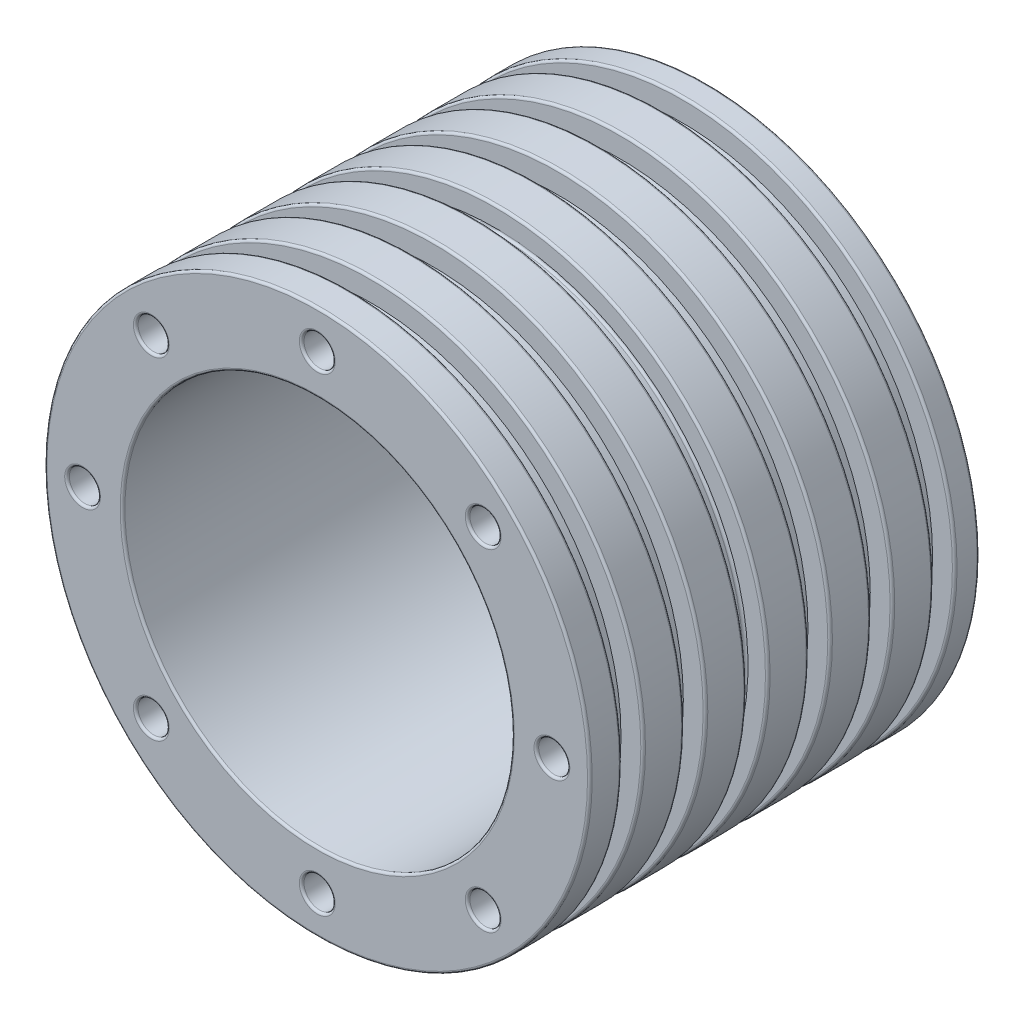
SolidWorks part; units mm, degrees
ref_plane "Front Plane" through (0, 0, 0) normal (0, 0, 1) x (1, 0, 0)
ref_plane "Top Plane" through (0, 0, 0) normal (0, 1, 0) x (1, 0, 0)
ref_plane "Right Plane" through (0, 0, 0) normal (1, 0, 0) x (0, 0, -1)
sketch "Sketch1" plane through (0, 0, 0) normal (0, 0, 1) x (1, 0, 0)
  circle A0 centre (0, 0) radius 250
  circle A1 centre (0, 0) radius 350
  dimension "D1" = 500
extrude "Boss-Extrude1" add sketch "Sketch1" along normal mid plane 500
sketch "Sketch2" plane through (0, 0, 0) normal (1, 0, 0) x (0, 0, -1)
  line L1 (-209.2281, 363.0254) -> (-181.625, 363.0254)
  line L2 (-209.2281, 363.0254) -> (-209.2281, 321.5619)
  line L3 (-209.2281, 321.5619) -> (-181.625, 321.5619)
  line L4 (-181.625, 363.0254) -> (-181.625, 321.5619)
sweep "Cut-Sweep1" cut profiles "Sketch2" path edge at (350, 0, 250)
pattern_linear "LPattern1" count 6 spacing 80 along (0, 0, -1) of "Cut-Sweep1"
sketch "Sketch3" plane through (0, 0, 250) normal (0, 0, 1) x (1, 0, 0)
  circle A0 centre (0, 301.2429) radius 20
extrude "Cut-Extrude1" cut sketch "Sketch3" against normal blind 500
pattern_circular "CirPattern1" count 8 over 360 about axis through (0, 0, 0) along (0, 0, 1) of "Cut-Extrude1"
fillet "Fillet1" radius 3 34 edges at (250, 0, -250) (20, 301.2429, -250) (-198.8687, 227.153, -250) (-301.2429, 20, -250) (-227.153, -198.8687, -250) (-20, -301.2429, -250) (198.8687, -227.153, -250) (301.2429, -20, -250) (227.153, 198.8687, -250) (250, 0, 250) (20, 301.2429, 250) (-198.8687, 227.153, 250) (-301.2429, 20, 250) (-227.153, -198.8687, 250) (-20, -301.2429, 250) (198.8687, -227.153, 250) (301.2429, -20, 250) (227.153, 198.8687, 250) (350, 0, -250) (-350, 0, -218.375) (-350, 0, -138.375) (350, 0, -190.7719) (-350, 0, -58.375) (350, 0, -110.7719) (-350, 0, 21.625) (350, 0, -30.7719) (-350, 0, 101.625) (350, 0, 49.2281) (-350, 0, 181.625) (350, 0, 129.2281) (350, 0, 250) (350, 0, 209.2281) (-321.5619, 0, -190.7719) (-321.5619, 0, 21.625)
